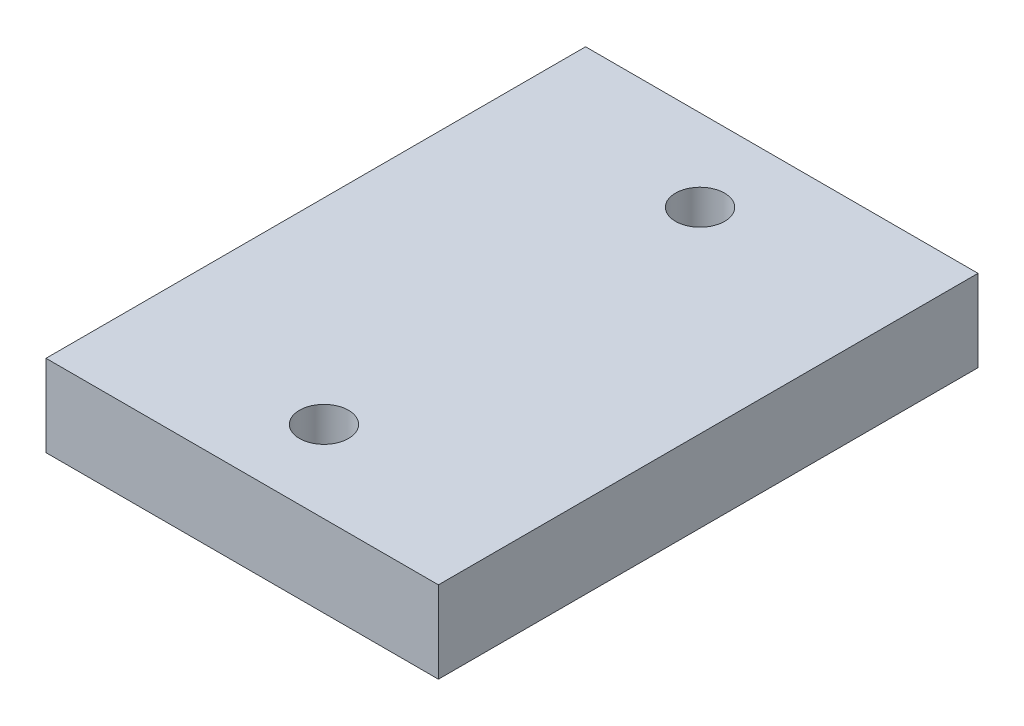
SolidWorks part; units mm, degrees
ref_plane "Front Plane" through (0, 0, 0) normal (0, 0, 1) x (1, 0, 0)
ref_plane "Top Plane" through (0, 0, 0) normal (0, 1, 0) x (1, 0, 0)
ref_plane "Right Plane" through (0, 0, 0) normal (1, 0, 0) x (0, 0, -1)
sketch "Sketch1" plane through (0, 0, 0) normal (0, 1, 0) x (1, 0, 0)
  line L1 (-12, 16.5) -> (12, 16.5)
  line L2 (-12, 16.5) -> (-12, -16.5)
  line L3 (-12, -16.5) -> (12, -16.5)
  line L4 (12, 16.5) -> (12, -16.5)
  line L5 (-12, 16.5) -> (12, -16.5) construction
  line L6 (-12, -16.5) -> (12, 16.5) construction
  circle A0 centre (0, 11.5) radius 1.5
  circle A1 centre (0, -11.5) radius 1.5
  point P0 (0, 0)
  point P10 (0, 0)
  dimension "D3" = 3
  dimension "D1" = 33
  dimension "D2" = 24
  dimension "D4" = 5
  dimension "D5" = 5
extrude "Boss-Extrude1" add sketch "Sketch1" along normal blind 5
